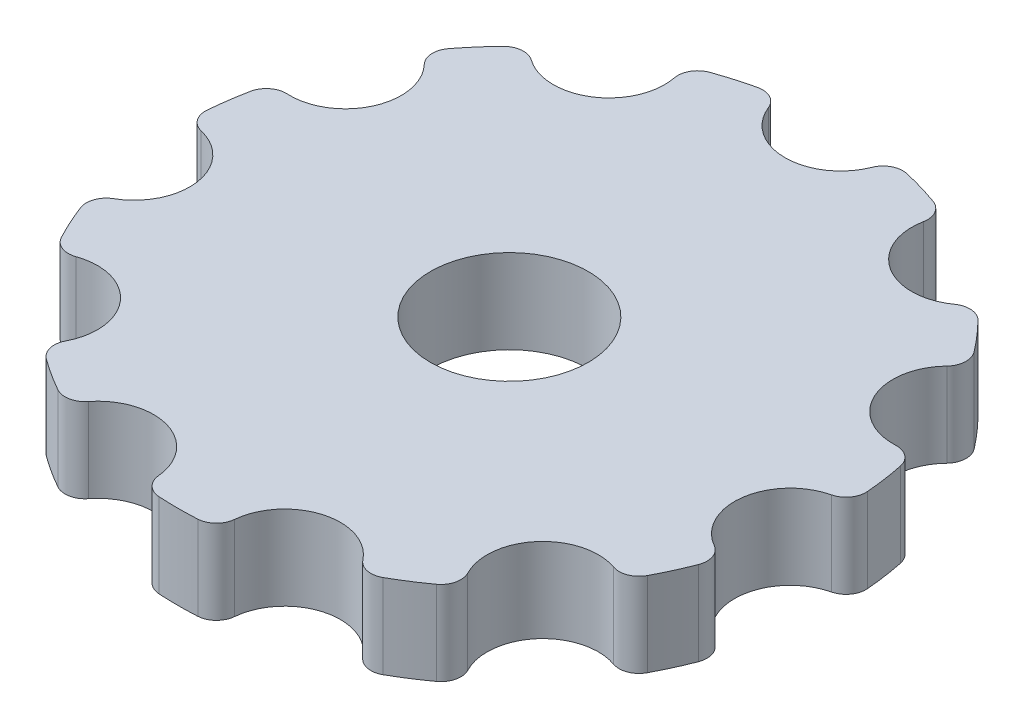
SolidWorks part; units mm, degrees
ref_plane "Front Plane" through (0, 0, 0) normal (0, 0, 1) x (1, 0, 0)
ref_plane "Top Plane" through (0, 0, 0) normal (0, 1, 0) x (1, 0, 0)
ref_plane "Right Plane" through (0, 0, 0) normal (1, 0, 0) x (0, 0, -1)
sketch "Sketch1" plane through (0, 0, 0) normal (0, 1, 0) x (1, 0, 0)
  circle A0 centre (0, 0) radius 12.5
  arc A1 (-1.9516, 11.7245) -> (1.9516, 11.7245) centre (0, 12.5) ccw
  arc A2 (2.8176, 12.1783) -> (1.9516, 11.7245) centre (2.6486, 11.4476) ccw
  arc A3 (-1.9516, 11.7245) -> (-2.8176, 12.1783) centre (-2.6486, 11.4476) ccw
  arc A4 (4.697, 10.9184) -> (4.2137, 11.7684) centre (3.9609, 11.0623) ccw
  arc A5 (4.697, 10.9184) -> (7.9805, 8.8082) centre (6.758, 10.5157) ccw
  arc A6 (8.9544, 8.7217) -> (7.9805, 8.8082) centre (8.4172, 8.1984) ccw
  arc A7 (9.8543, 6.6458) -> (9.9073, 7.6221) centre (9.3128, 7.1647) ccw
  arc A8 (9.8543, 6.6458) -> (11.4757, 3.0953) centre (11.3704, 5.1927) ccw
  arc A9 (12.2483, 2.496) -> (11.4757, 3.0953) centre (11.5134, 2.3463) ccw
  arc A10 (11.8829, 0.2631) -> (12.4553, 1.0558) centre (11.708, 0.9925) ccw
  arc A11 (11.8829, 0.2631) -> (11.3275, -3.6003) centre (12.3728, -1.7789) ccw
  arc A12 (11.6533, -4.5221) -> (11.3275, -3.6003) centre (10.9541, -4.2508) ccw
  arc A13 (10.1388, -6.203) -> (11.0489, -5.8457) centre (10.386, -5.4949) ccw
  arc A14 (10.1388, -6.203) -> (7.5828, -9.1529) centre (9.4469, -8.1858) ccw
  arc A15 (7.3586, -10.1045) -> (7.5828, -9.1529) centre (6.9171, -9.4982) ccw
  arc A16 (5.1757, -10.6998) -> (6.1345, -10.8912) centre (5.7665, -10.2377) ccw
  arc A17 (5.1757, -10.6998) -> (1.4307, -11.7994) centre (3.5217, -11.9937) ccw
  arc A18 (0.7275, -12.4788) -> (1.4307, -11.7994) centre (0.6839, -11.7301) ccw
  arc A19 (-1.4307, -11.7994) -> (-0.7275, -12.4788) centre (-0.6839, -11.7301) ccw
  arc A20 (-1.4307, -11.7994) -> (-5.1757, -10.6998) centre (-3.5217, -11.9937) ccw
  arc A21 (-6.1345, -10.8912) -> (-5.1757, -10.6998) centre (-5.7665, -10.2377) ccw
  arc A22 (-7.5828, -9.1529) -> (-7.3586, -10.1045) centre (-6.9171, -9.4982) ccw
  arc A23 (-7.5828, -9.1529) -> (-10.1388, -6.203) centre (-9.4469, -8.1858) ccw
  arc A24 (-11.0489, -5.8457) -> (-10.1388, -6.203) centre (-10.386, -5.4949) ccw
  arc A25 (-11.3275, -3.6003) -> (-11.6533, -4.5221) centre (-10.9541, -4.2508) ccw
  arc A26 (-11.3275, -3.6003) -> (-11.8829, 0.2631) centre (-12.3728, -1.7789) ccw
  arc A27 (-12.4553, 1.0558) -> (-11.8829, 0.2631) centre (-11.708, 0.9925) ccw
  arc A28 (-11.4757, 3.0953) -> (-12.2483, 2.496) centre (-11.5134, 2.3463) ccw
  arc A29 (-11.4757, 3.0953) -> (-9.8543, 6.6458) centre (-11.3704, 5.1927) ccw
  arc A30 (-9.9073, 7.6221) -> (-9.8543, 6.6458) centre (-9.3128, 7.1647) ccw
  arc A31 (-7.9805, 8.8082) -> (-8.9544, 8.7217) centre (-8.4172, 8.1984) ccw
  arc A32 (-7.9805, 8.8082) -> (-4.697, 10.9184) centre (-6.758, 10.5157) ccw
  arc A33 (-4.2137, 11.7684) -> (-4.697, 10.9184) centre (-3.9609, 11.0623) ccw
  circle A34 centre (0, 0) radius 2.975
  point P83 (0, 0)
  dimension "D1" = 25
  dimension "D2" = 4.2
  dimension "D3" = 1.5
  dimension "D4" = 5.95
extrude "Boss-Extrude1" add sketch "Sketch1" along normal blind 3.175 contours A0 A33 A32 A31 A30 A29 A28 A27 A26 A25 A24 A23 A22 A21 A20 A19 A18 A17 A16 A15 A14 A13 A12 A11 A10 A9 A8 A7 A6 A5 A4 A2 A1 A3 A34
